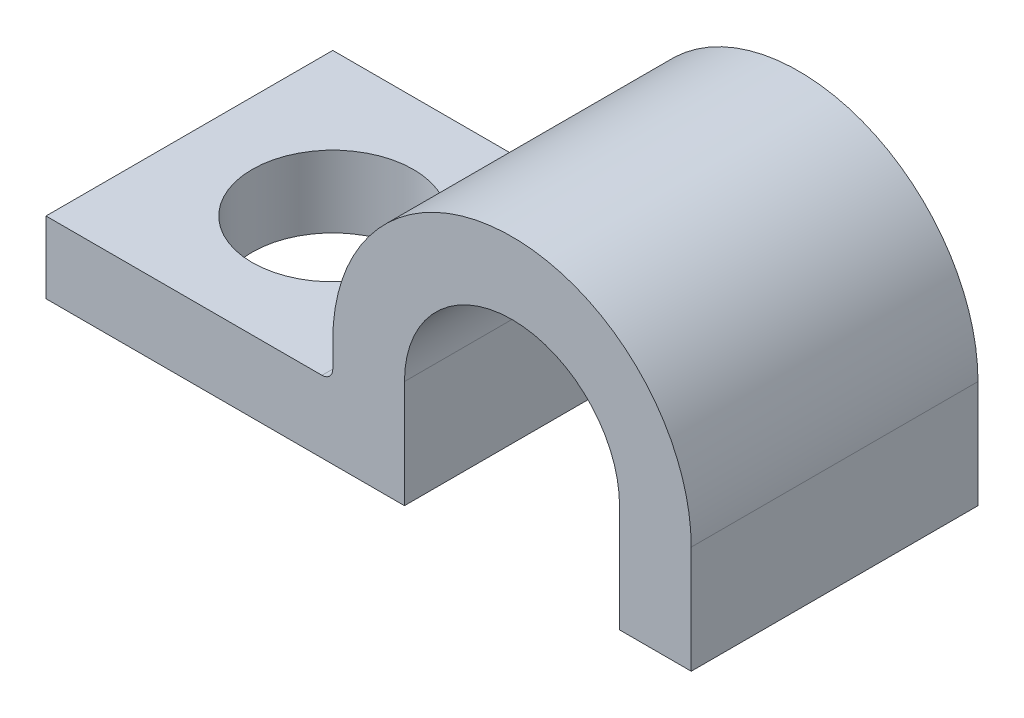
SolidWorks part; units mm, degrees
ref_plane "Plan1" through (0, 0, 0) normal (0, 0, 1) x (1, 0, 0)
ref_plane "Plan2" through (0, 0, 0) normal (0, 1, 0) x (1, 0, 0)
ref_plane "Plan3" through (0, 0, 0) normal (1, 0, 0) x (0, 0, -1)
sketch "Esquisse1" plane through (0, 0, 0) normal (0, 0, 1) x (1, 0, 0)
  line L0 (0, 0) -> (10, 0)
  line L1 (10, 0) -> (10, 3)
  line L2 (16, 3) -> (16, 0)
  line L3 (18, 3) -> (18, 0)
  line L4 (8, 2) -> (8, 3)
  line L5 (0, 2) -> (8, 2)
  line L6 (0, 0) -> (0, 2)
  line L7 (18, 0) -> (16, 0)
  arc A0 (10, 3) -> (16, 3) centre (13, 3) cw
  arc A1 (8, 3) -> (18, 3) centre (13, 3) cw
  dimension "D2" = 3
  dimension "D3" = 10
  dimension "D4" = 3
  dimension "D1" = 2
extrude "Base-Extrusion" add sketch "Esquisse1" along normal blind 8
sketch "Esquisse2" plane through (0, 2, 0) normal (0, 1, 0) x (-1, 0, 0)
  line L0 (0, 4) -> (-4, 4) construction
  line L1 (0, 8) -> (0, 0) construction
  circle A0 centre (-4, 4) radius 2.25
  dimension "D1" = 4.5
  dimension "D2" = 4
extrude "Enlèv. mat.-Extru.1" cut sketch "Esquisse2" against normal through all
fillet "Congé1" radius 0.3
equation "\"D4@Esquisse1\" = \"D2@Esquisse1\""
